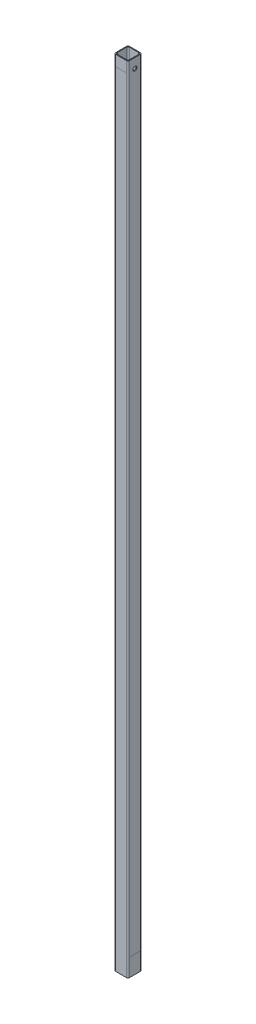
SolidWorks part; units mm, degrees
material "Carbon Fiber"
ref_plane "Front Plane" through (0, 0, 0) normal (0, 0, 1) x (1, 0, 0)
ref_plane "Top Plane" through (0, 0, 0) normal (0, 1, 0) x (1, 0, 0)
ref_plane "Right Plane" through (0, 0, 0) normal (1, 0, 0) x (0, 0, -1)
sketch "Sketch1" plane through (0, 0, 0) normal (0, 1, 0) x (1, 0, 0)
  line L1 (-11.3411, -11.3411) -> (11.3411, -11.3411)
  line L2 (-11.3411, -11.3411) -> (-11.3411, 11.3411)
  line L3 (-11.3411, 11.3411) -> (11.3411, 11.3411)
  line L4 (11.3411, -11.3411) -> (11.3411, 11.3411)
  line L5 (-11.3411, -11.3411) -> (11.3411, 11.3411) construction
  line L6 (-11.3411, 11.3411) -> (11.3411, -11.3411) construction
  line L7 (-10.0711, -10.0711) -> (10.0711, -10.0711)
  line L8 (-10.0711, -10.0711) -> (-10.0711, 10.0711)
  line L9 (-10.0711, 10.0711) -> (10.0711, 10.0711)
  line L10 (10.0711, -10.0711) -> (10.0711, 10.0711)
  line L11 (-10.0711, -10.0711) -> (10.0711, 10.0711) construction
  line L12 (-10.0711, 10.0711) -> (10.0711, -10.0711) construction
  point P0 (0, 0)
  point P6 (0, 0)
  dimension "D1" = 1.27
  dimension "D3" = 20.1422
extrude "Boss-Extrude1" add sketch "Sketch1" along normal blind 1303.02
fillet "Fillet1" radius 2.54 8 edges at (-11.3411, 651.51, 11.3411) (11.3411, 651.51, 11.3411) (11.3411, 651.51, -11.3411) (-11.3411, 651.51, -11.3411) (10.0711, 651.51, 10.0711) (10.0711, 651.51, -10.0711) (-10.0711, 651.51, -10.0711) (-10.0711, 651.51, 10.0711)
sketch "Sketch2" plane through (0, 0, 11.3411) normal (0, 0, 1) x (1, 0, 0)
  line L0 (-8.8011, 1303.02) -> (-8.8011, 0) construction
  line L1 (-8.8011, 1285.4178) -> (8.8011, 1285.4178)
  line L2 (-8.8011, 1285.4178) -> (-8.8011, 1303.02)
  line L3 (-8.8011, 1303.02) -> (8.8011, 1303.02)
  line L4 (8.8011, 1285.4178) -> (8.8011, 1303.02)
  line L5 (-8.8011, 1285.4178) -> (8.8011, 1303.02) construction
  line L6 (-8.8011, 1303.02) -> (8.8011, 1285.4178) construction
  line L7 (8.8011, 0) -> (8.8011, 1303.02) construction
  line L9 (-8.8011, 1303.02) -> (8.8011, 1303.02) construction
  point P0 (0, 1294.2189)
sketch "Sketch3" plane through (0, 0, 0) normal (0, -1, 0) x (1, 0, 0)
  line L4 (8.8011, 11.3411) -> (-8.8011, 11.3411)
  line L5 (-11.3411, 8.8011) -> (-11.3411, -8.8011)
  line L6 (-8.8011, -11.3411) -> (8.8011, -11.3411)
  line L7 (11.3411, -8.8011) -> (11.3411, 8.8011)
  line L9 (-11.3411, 8.8011) -> (-11.3411, -8.8011)
  line L10 (-8.8011, -11.3411) -> (8.8011, -11.3411)
  line L11 (11.3411, -8.8011) -> (11.3411, 8.8011)
  line L13 (8.8011, 11.3411) -> (-8.8011, 11.3411)
  arc A4 (-8.8011, 11.3411) -> (-11.3411, 8.8011) centre (-8.8011, 8.8011) ccw
  arc A5 (-11.3411, -8.8011) -> (-8.8011, -11.3411) centre (-8.8011, -8.8011) ccw
  arc A6 (8.8011, -11.3411) -> (11.3411, -8.8011) centre (8.8011, -8.8011) ccw
  arc A7 (11.3411, 8.8011) -> (8.8011, 11.3411) centre (8.8011, 8.8011) ccw
  arc A8 (-8.8011, 11.3411) -> (-11.3411, 8.8011) centre (-8.8011, 8.8011) ccw
  arc A9 (-11.3411, -8.8011) -> (-8.8011, -11.3411) centre (-8.8011, -8.8011) ccw
  arc A10 (8.8011, -11.3411) -> (11.3411, -8.8011) centre (8.8011, -8.8011) ccw
  arc A11 (11.3411, 8.8011) -> (8.8011, 11.3411) centre (8.8011, 8.8011) ccw
  dimension "D1" = 0
extrude "Boss-Extrude2" [suppressed] add sketch "Sketch3" against normal blind 2.54
hole_wizard "1/4 (0.25) Diameter Hole1" [suppressed] positions "Sketch4" profile "Sketch5" hole size "1/4" standard "ANSI Inch"
sketch "Sketch4" plane through (0, 0, 0) normal (0, -1, 0) x (-1, 0, 0)
  point P0 (0, 0)
sketch "Sketch5" plane through (0, 0, 0) normal (1, 0, 0) x (0, 0, -1)
  line L0 (0, 0) -> (0, 1303.02)
  line L1 (0, 1303.02) -> (3.175, 1303.02)
  line L2 (3.175, 1303.02) -> (3.175, 0)
  line L5 (3.175, 0) -> (0, 0)
  line L11 (0, -6.35) -> (0, 107.95) construction
  dimension "Thru Hole Dia." = 6.35
  dimension "Thru Hole Depth" = 1303.02
hole_wizard "1/4 Clearance Hole1" positions "Sketch6" profile "Sketch7" hole size "1/4" standard "ANSI Inch" end condition through all
sketch "Sketch6" plane through (11.3411, 0, 0) normal (1, 0, 0) x (0, 0, -1)
  line L0 (-8.8011, 1303.02) -> (8.8011, 1303.02) construction
  point P0 (0, 1287.145)
  dimension "D1" = 15.875
sketch "Sketch7" plane through (11.3411, 1287.145, 0) normal (0, 1, 0) x (0, 0, -1)
  line L0 (0, 0) -> (0, 22.6822)
  line L1 (0, 22.6822) -> (3.3782, 22.6822)
  line L2 (3.3782, 22.6822) -> (3.3782, 0)
  line L5 (3.3782, 0) -> (0, 0)
  line L11 (0, -6.35) -> (0, 107.95) construction
  dimension "Thru Hole Dia." = 6.7564
  dimension "Thru Hole Depth" = 22.6822
sketch "Sketch8" plane through (0, 0, -11.3411) normal (0, 0, -1) x (-1, 0, 0)
  line L0 (-8.8011, 1303.02) -> (-8.8011, 0) construction
  line L1 (-8.8011, 241.3) -> (8.8011, 241.3)
  line L2 (-8.8011, 241.3) -> (-8.8011, 258.9022)
  line L3 (-8.8011, 258.9022) -> (8.8011, 258.9022)
  line L4 (8.8011, 241.3) -> (8.8011, 258.9022)
  line L5 (8.8011, 0) -> (8.8011, 1303.02) construction
  dimension "D1" = 241.3
split line "Split Line2"
split line "Split Line3"
sketch "Sketch9" plane through (11.3411, 0, 0) normal (1, 0, 0) x (0, 0, -1)
  line L0 (8.8011, 0) -> (8.8011, 1303.02) construction
  line L1 (-8.8011, 0) -> (8.8011, 0)
  line L2 (-8.8011, 0) -> (-8.8011, 29.0055)
  line L3 (-8.8011, 29.0055) -> (8.8011, 29.0055)
  line L4 (8.8011, 0) -> (8.8011, 29.0055)
split line "Split Line4"
